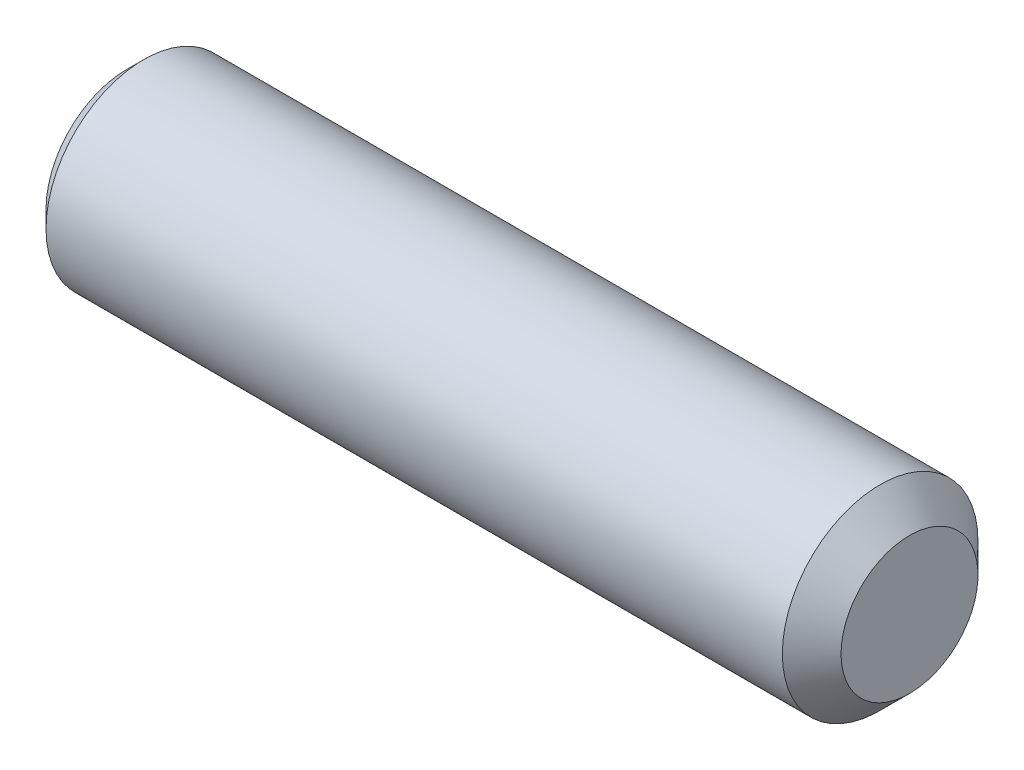
SolidWorks part; units mm, degrees
ref_plane "Front" through (0, 0, 0) normal (0, 0, 1) x (1, 0, 0)
ref_plane "Top" through (0, 0, 0) normal (0, 1, 0) x (1, 0, 0)
ref_plane "Right" through (0, 0, 0) normal (1, 0, 0) x (0, 0, -1)
sketch "Sketch1" plane through (0, 0, 0) normal (0, 0, 1) x (1, 0, 0)
  line L0 (0, 0) -> (20, 0)
  line L1 (20, 0) -> (20, 1.75)
  line L2 (20, 1.75) -> (19.25, 2.5)
  line L3 (19.25, 2.5) -> (0.433, 2.5)
  line L4 (0.433, 2.5) -> (0, 2.067)
  line L5 (0, 2.067) -> (0, 0)
  line L6 (-10.745, 0) -> (0.8952, 0) construction
  dimension "D1" = 45
  dimension "l" = 20
  dimension "D2" = 45
  dimension "dp" = 3.5
  dimension "d" = 5
  dimension "df" = 4.134
revolve "Base" add sketch "Sketch1" angle 360 about L6
cosmetic thread "ThreadCosmetic1" [suppressed] parameters "D2"=4.134
sketch "Sketch2" plane through (0, -0.0219, 0.0101) normal (-1, 0, 0) x (0, 0, 1)
  line L1 (1.4332, 0.0219) -> (0.7115, 1.2719)
  line L2 (0.7115, 1.2719) -> (-0.7318, 1.2719)
  line L3 (-0.7318, 1.2719) -> (-1.4535, 0.0219)
  line L4 (-1.4535, 0.0219) -> (-0.7318, -1.2281)
  line L5 (-0.7318, -1.2281) -> (0.7115, -1.2281)
  line L6 (0.7115, -1.2281) -> (1.4332, 0.0219)
  circle A0 centre (-0.0101, 0.0219) radius 1.25 construction
  dimension "s" = 2.5
extrude "HexagonSocket" cut sketch "Sketch2" against normal blind 2
sketch "Sketch3" plane through (0, 0, 0) normal (0, 0, 1) x (1, 0, 0)
  line L0 (-3.1441, 0) -> (0.1622, 0) construction
  line L2 (2, 1.25) -> (2.7217, 0)
  line L4 (2, 1.25) -> (2, 0)
  line L5 (2, 0) -> (2.7217, 0)
  dimension "D1" = 60
revolve "Cut-Revolve1" cut sketch "Sketch3" angle 360 about L0
sketch "Sketch4" plane through (0, 0, 0) normal (0, 0, 1) x (1, 0, 0)
  line L0 (0.433, 2.125) -> (0.6495, 2.5)
  line L1 (0.6495, 2.5) -> (0.6495, 2.933)
  line L2 (0.6495, 2.933) -> (0.2165, 2.933)
  line L3 (0.2165, 2.933) -> (0.2165, 2.5)
  line L4 (0.2165, 2.5) -> (0.433, 2.125)
  line L5 (0, 0) -> (0.9616, 0) construction
  line L6 (0.433, 2.5) -> (0.433, -2.5) construction
  dimension "D1" = 5
  dimension "D2" = 0.433
revolve "Cut-Revolve10" [suppressed] cut sketch "Sketch4" angle 360 about L5
pattern_linear "LPattern10" [suppressed] count 38 spacing 0.5196 along (1, 0, 0)
equation "\"df@Sketch1\" = \"D2@ThreadCosmetic1\""
equation "\"D1@Sketch4\" = \"d@Sketch1\""
equation "\"D2@Sketch4\" =  ( \"d@Sketch1\" - \"D2@ThreadCosmetic1\" )  / 2"
equation "\"D3@LPattern10\" = \"D2@Sketch4\" * 1.2"
equation "\"D1@LPattern10\" = (  \"l@Sketch1\" -  ( \"d@Sketch1\" - \"df@Sketch1\" )  / 2 )  / \"D3@LPattern10\""
